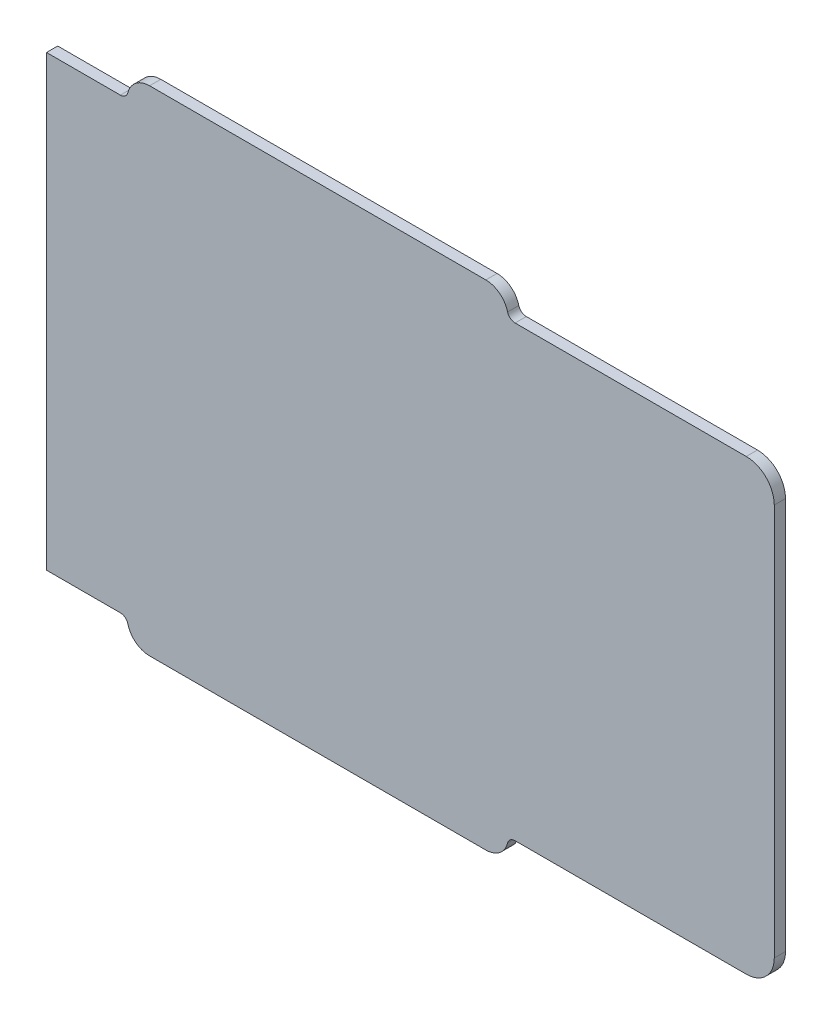
SolidWorks part; units mm, degrees
ref_plane "Front Plane" through (0, 0, 0) normal (0, 0, 1) x (1, 0, 0)
ref_plane "Top Plane" through (0, 0, 0) normal (0, 1, 0) x (1, 0, 0)
ref_plane "Right Plane" through (0, 0, 0) normal (1, 0, 0) x (0, 0, -1)
sketch "Sketch1" plane through (0, 0, 0) normal (0, 0, 1) x (1, 0, 0)
  line L0 (120.3, 160) -> (146.6617, 160)
  line L1 (10, 160) -> (146.6617, 160) construction
  line L2 (157.08, 168.1) -> (277.08, 168.1) construction
  line L3 (157.08, 168.1) -> (277.08, 168.1)
  line L4 (287.4983, 160) -> (370, 160)
  line L5 (380, 150) -> (380, 10)
  line L6 (287.4983, 0) -> (370, 0) construction
  line L7 (370, 0) -> (287.4983, 0)
  line L8 (277.08, -8.1) -> (157.08, -8.1)
  line L9 (10, 0) -> (146.6617, 0) construction
  line L10 (120.3, 160) -> (120.3, 0)
  line L11 (120.3, 0) -> (146.6617, 0)
  line L12 (120, 0) -> (120, 160) construction
  arc A0 (146.6617, 160) -> (149.3269, 162.0721) centre (146.6617, 162.75) ccw
  arc A1 (157.08, 168.1) -> (149.3269, 162.0721) centre (157.08, 160.1) ccw construction
  arc A2 (149.3269, 162.0721) -> (157.08, 168.1) centre (157.08, 160.1) cw
  arc A3 (277.08, 168.1) -> (284.8331, 162.0721) centre (277.08, 160.1) cw
  arc A4 (284.8331, 162.0721) -> (287.4983, 160) centre (287.4983, 162.75) ccw construction
  arc A5 (284.8331, 162.0721) -> (287.4983, 160) centre (287.4983, 162.75) ccw
  arc A6 (370, 160) -> (380, 150) centre (370, 150) cw
  arc A7 (380, 150) -> (370, 160) centre (370, 150) ccw construction
  arc A8 (380, 10) -> (370, 0) centre (370, 10) cw
  arc A9 (287.4983, 0) -> (284.8331, -2.0721) centre (287.4983, -2.75) ccw
  arc A10 (277.08, -8.1) -> (284.8331, -2.0721) centre (277.08, -0.1) ccw construction
  arc A11 (284.8331, -2.0721) -> (277.08, -8.1) centre (277.08, -0.1) cw
  arc A12 (157.08, -8.1) -> (149.3269, -2.0721) centre (157.08, -0.1) cw
  arc A13 (149.3269, -2.0721) -> (157.08, -8.1) centre (157.08, -0.1) ccw construction
  arc A14 (149.3269, -2.0721) -> (146.6617, 0) centre (146.6617, -2.75) ccw
  point P66 (0, 0)
  dimension "D1" = 0.3
extrude "Boss-Extrude1" add sketch "Sketch1" along normal blind 4 contours L3 A3 A5 L4 A6 L5 A8 L7 A9 A11 L8 A12 A14 L11 L10 L0 A0 A2
sketch "Sketch2" plane through (0, 0, 0) normal (0, 0, -1) x (-1, 0, 0)
  circle A0 centre (-126.25, 8.75) radius 2.75
  circle A1 centre (-126.25, 151.25) radius 2.75
  circle A2 centre (-370, 10) radius 2.75
  circle A3 centre (-370, 150) radius 2.75
extrude "Cut-Extrude1" cut sketch "Sketch2" against normal blind 3
sketch "Sketch3" plane through (0, 0, 0) normal (0, 0, -1) x (-1, 0, 0)
  circle A0 centre (-157.08, -0.1) radius 2.35
  circle A1 centre (-157.08, -0.1) radius 2.75 construction
  circle A2 centre (-157.08, 160.1) radius 2.35
  circle A3 centre (-277.08, 160.1) radius 2.35
  circle A4 centre (-277.08, -0.1) radius 2.35
  circle A5 centre (-277.08, -0.1) radius 2.75 construction
  circle A6 centre (-277.08, 160.1) radius 2.75 construction
  circle A7 centre (-157.08, 160.1) radius 2.75 construction
  dimension "D1" = 0.4
  dimension "D2" = 0.4
  dimension "D3" = 0.4
  dimension "D4" = 0.4
extrude "Boss-Extrude2" add sketch "Sketch3" along normal blind 4
chamfer "Chamfer1" distance 1 angle 45 4 edges at (154.73, -0.1, -4) (274.73, -0.1, -4) (274.73, 160.1, -4) (154.73, 160.1, -4)
sketch "Sketch4" plane through (0, 0, 0) normal (0, 0, -1) x (-1, 0, 0)
  line L0 (-364.25, 10) -> (-364.25, 3)
  line L1 (-281.003, 3) -> (-364.3091, 3) construction
  line L2 (-364.25, 3) -> (-272.08, 3)
  line L3 (-272.08, 3) -> (-272.08, -5.1)
  line L4 (-272.08, -5.1) -> (-162.08, -5.1)
  line L5 (-162.08, -5.1) -> (-162.08, 3)
  line L6 (-162.08, 3) -> (-132, 3)
  line L7 (-132, 3) -> (-132, 8.75)
  line L8 (-126.25, 14.5) -> (-122.8675, 14.5)
  line L9 (-126.25, 14.5) -> (-111.25, 14.5) construction
  line L10 (-122.8675, 14.5) -> (-122.8675, 145.5)
  line L11 (-126.25, 145.5) -> (-111.25, 145.5) construction
  line L12 (-122.8675, 145.5) -> (-126.25, 145.5)
  line L13 (-132, 151.25) -> (-132, 157)
  line L14 (-132, 157) -> (-162.08, 157)
  line L15 (-162.08, 157) -> (-162.08, 165.1)
  line L16 (-162.08, 165.1) -> (-272.08, 165.1)
  line L17 (-272.08, 165.1) -> (-272.08, 157)
  line L18 (-272.08, 157) -> (-364.25, 157)
  line L19 (-281.003, 157) -> (-364.3091, 157) construction
  line L20 (-364.25, 157) -> (-364.25, 150)
  line L21 (-370, 144.25) -> (-374.0235, 144.25)
  line L22 (-377, 15.6909) -> (-377, 144.3091) construction
  line L23 (-377, 141.2702) -> (-377, 18.7472)
  line L24 (-374, 15.75) -> (-370, 15.75)
  line L25 (-377, 141.25) -> (-374, 141.25)
  line L26 (-374, 141.25) -> (-374, 144.25)
  line L27 (-374, 15.75) -> (-374, 18.75)
  line L28 (-374, 18.75) -> (-377, 18.75)
  arc A0 (-132, 8.75) -> (-126.25, 14.5) centre (-126.25, 8.75) cw
  arc A1 (-126.25, 14.5) -> (-132, 8.75) centre (-126.25, 8.75) ccw construction
  arc A2 (-126.25, 145.5) -> (-132, 151.25) centre (-126.25, 151.25) cw
  arc A3 (-132, 151.25) -> (-126.25, 145.5) centre (-126.25, 151.25) ccw construction
  arc A4 (-364.25, 150) -> (-370, 144.25) centre (-370, 150) cw
  arc A5 (-370, 144.25) -> (-364.25, 150) centre (-370, 150) ccw construction
  arc A6 (-370, 15.75) -> (-364.25, 10) centre (-370, 10) cw
  arc A7 (-364.25, 10) -> (-370, 15.75) centre (-370, 10) ccw construction
  point P54 (0, 0)
  dimension "D1" = 3
  dimension "D2" = 3
  dimension "D3" = 3
  dimension "D4" = 0
extrude "Cut-Extrude2" cut sketch "Sketch4" against normal blind 2.5 contours L24 A6 L0 L2 L3 L4 L5 L6 L7 A0 L8 L10 L12 A2 L13 L14 L15 L16 L17 L18 L20 A4 L21 L23
sketch "Sketch5" plane through (0, 0, 2.5) normal (0, 0, -1) x (-1, 0, 0)
sketch "Sketch6" plane through (0, 0, 0) normal (0, 0, -1) x (-1, 0, 0)
  line L0 (-374, 141.25) -> (-374, 144.25) construction
  line L1 (-374, 18.75) -> (-376.7, 18.75)
  line L2 (-374, 18.75) -> (-374, 16.05)
  line L3 (-374, 16.05) -> (-376.7, 16.05)
  line L4 (-376.7, 18.75) -> (-376.7, 16.05)
  line L5 (-374, 141.25) -> (-376.7, 141.25)
  line L6 (-374, 141.25) -> (-374, 143.95)
  line L7 (-374, 143.95) -> (-376.7, 143.95)
  line L8 (-376.7, 141.25) -> (-376.7, 143.95)
  line L9 (-377, 15.6909) -> (-377, 144.3091) construction
  line L10 (-376.9516, 144.25) -> (-370, 144.25) construction
  line L11 (-377, 141.25) -> (-374, 141.25) construction
  line L12 (-376.9516, 15.75) -> (-370, 15.75) construction
  dimension "D1" = 0.3
  dimension "D2" = 0.3
  dimension "D3" = 0
  dimension "D4" = 0.3
  dimension "D5" = 0.3
extrude "Boss-Extrude3" add sketch "Sketch6" along normal blind 4
chamfer "Chamfer2" distance 0.74 angle 45 6 edges at (376.7, 142.6, -4) (375.35, 143.95, -4) (376.7, 143.95, -2) (376.7, 16.05, -2) (375.35, 16.05, -4) (376.7, 17.4, -4)
